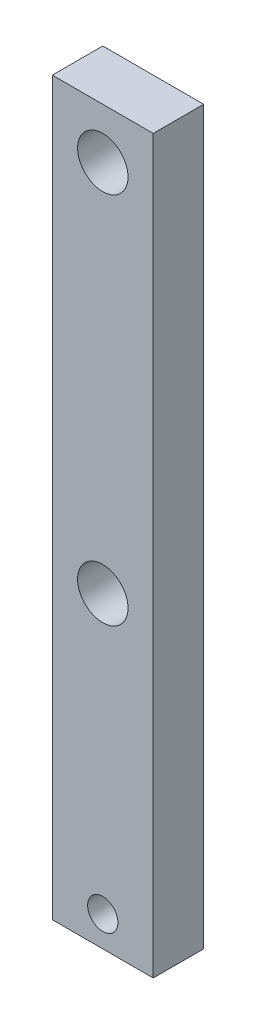
SolidWorks part; units mm, degrees
ref_plane "Front Plane" through (0, 0, 0) normal (0, 0, 1) x (1, 0, 0)
ref_plane "Top Plane" through (0, 0, 0) normal (0, 1, 0) x (1, 0, 0)
ref_plane "Right Plane" through (0, 0, 0) normal (1, 0, 0) x (0, 0, -1)
sketch "Sketch1" plane through (0, 0, 0) normal (0, 0, 1) x (1, 0, 0)
  line L1 (-10, 72.5) -> (0, 72.5)
  line L2 (-10, 72.5) -> (-10, 0)
  line L3 (-10, 0) -> (0, 0)
  line L4 (0, 72.5) -> (0, 0)
  dimension "D1" = 72.5
  dimension "D2" = 10
extrude "Boss-Extrude1" add sketch "Sketch1" along normal blind 5
sketch "Sketch2" plane through (0, 0, 5) normal (0, 0, 1) x (1, 0, 0)
  line L0 (0, 72.5) -> (-10, 72.5) construction
  line L1 (-10, 72.5) -> (-10, 0) construction
  circle A0 centre (-5, 67.5) radius 2.5
  dimension "D1" = 5
  dimension "D2" = 5
  dimension "D3" = 5
extrude "Cut-Extrude1" cut sketch "Sketch2" against normal through all contours A0
sketch "Sketch3" plane through (0, 0, 5) normal (0, 0, 1) x (1, 0, 0)
  line L0 (-10, 0) -> (0, 0) construction
  line L1 (-10, 72.5) -> (-10, 0) construction
  line L2 (0, 0) -> (0, 72.5) construction
  circle A0 centre (-5, 3) radius 1.5
  circle A1 centre (-5, 30.5) radius 2.5
  dimension "D1" = 3
  dimension "D4" = 5
  dimension "D2" = 3
  dimension "D3" = 5
  dimension "D5" = 27.5
  dimension "D6" = 5
extrude "Cut-Extrude2" cut sketch "Sketch3" against normal through all
